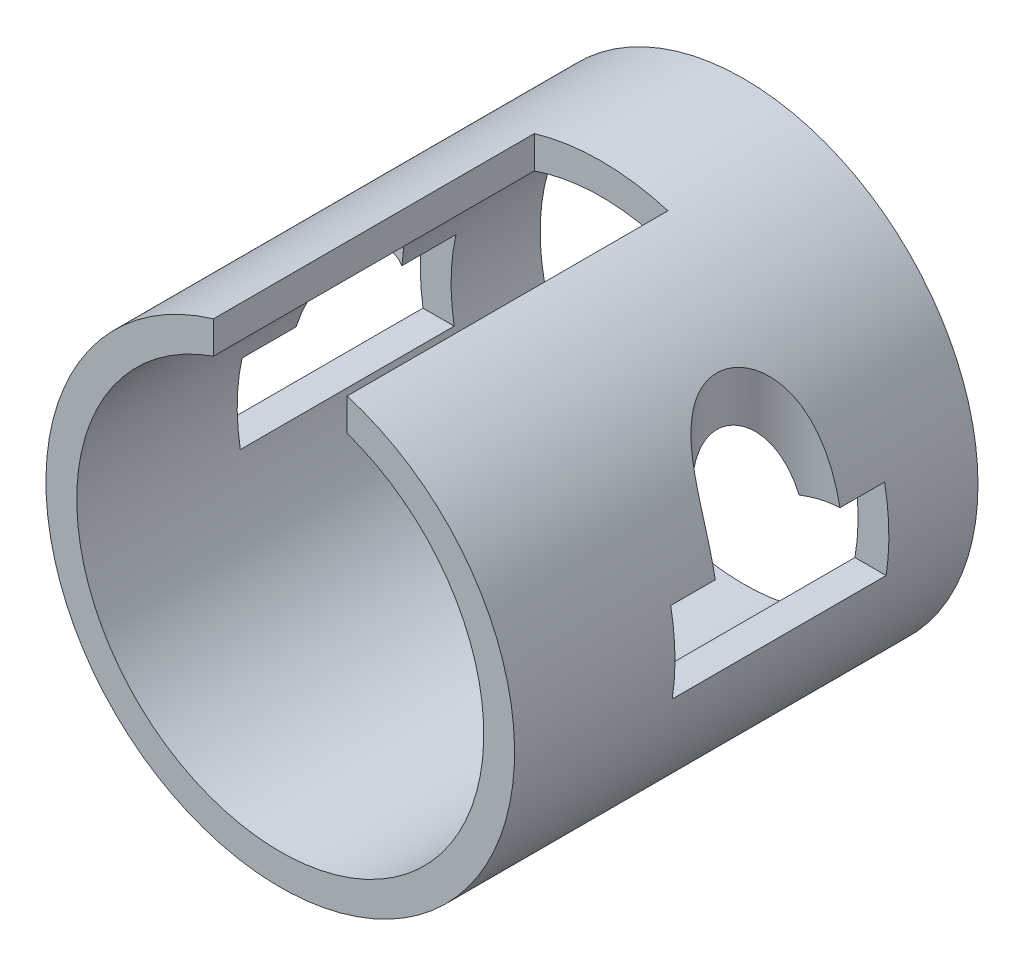
SolidWorks part; units mm, degrees
material "PVC Rigid"
ref_plane "Front Plane" through (0, 0, 0) normal (0, 0, 1) x (1, 0, 0)
ref_plane "Top Plane" through (0, 0, 0) normal (0, 1, 0) x (1, 0, 0)
ref_plane "Right Plane" through (0, 0, 0) normal (1, 0, 0) x (0, 0, -1)
sketch "Sketch1" plane through (0, 0, 0) normal (0, 0, 1) x (1, 0, 0)
  circle A0 centre (0, 0) radius 83.4771
  circle A2 centre (0, 0) radius 72.5043
  point P3 (0, 0)
  point P10 (0, 0)
  dimension "D1" = 10.9728
  dimension "D2" = 145.0086
extrude "Boss-Extrude1" add sketch "Sketch1" along normal mid plane 165.1
sketch "Sketch2" plane through (0, 0, 0) normal (0, 1, 0) x (1, 0, 0)
  line L0 (-23.8125, 31.75) -> (0, 0) construction
  line L1 (-23.8125, 31.75) -> (23.8125, 31.75)
  line L2 (-23.8125, 31.75) -> (-23.8125, -82.55)
  line L3 (-23.8125, -82.55) -> (23.8125, -82.55)
  line L4 (23.8125, 31.75) -> (23.8125, -82.55)
  line L5 (-23.8125, 31.75) -> (23.8125, -82.55) construction
  line L6 (-23.8125, -82.55) -> (23.8125, 31.75) construction
  line L7 (0, 0) -> (23.8125, 31.75) construction
  line L8 (-83.4771, -82.55) -> (83.4771, -82.55) construction
  point P0 (0, -25.4)
  dimension "D1" = 47.625
  dimension "D2" = 0
  dimension "D3" = 114.3
extrude "Cut-Extrude1" cut sketch "Sketch2" along normal through all
sketch "Sketch3" plane through (0, 0, 0) normal (1, 0, 0) x (0, 0, -1)
  line L0 (-82.55, 80.0087) -> (-82.55, -83.4771) construction
  line L1 (50.8, 12.7) -> (-25.4, 12.7) construction
  line L2 (50.8, 12.7) -> (50.8, -12.7)
  line L3 (50.8, -12.7) -> (-25.4, -12.7)
  line L4 (-25.4, 12.7) -> (-25.4, -12.7)
  line L5 (50.8, 12.7) -> (-25.4, -12.7) construction
  line L6 (50.8, -12.7) -> (-25.4, 12.7) construction
  line L7 (-25.4, 12.7) -> (0, 0) construction
  line L8 (0, 0) -> (-25.4, -12.7) construction
  line L9 (50.8, 12.7) -> (-25.4, 12.7)
  point P0 (12.7, 0)
  dimension "D1" = 57.15
  dimension "D2" = 76.2
  dimension "D3" = 25.4
extrude "Cut-Extrude2" cut sketch "Sketch3" against normal through all both and the other way through all
sketch "Sketch4" plane through (0, -12.7, 0) normal (0, 1, 0) x (1, 0, 0)
  line L0 (-71.3834, 12.7) -> (-82.5054, 12.7) construction
  line L1 (-71.3834, -25.4) -> (-71.3834, 50.8) construction
  line L2 (71.3834, 12.7) -> (82.5054, 12.7) construction
  line L3 (71.3834, 50.8) -> (71.3834, -25.4) construction
  line L4 (-82.5054, -25.4) -> (-82.5054, 50.8) construction
  circle A0 centre (-82.5054, 12.7) radius 22.225
  circle A1 centre (82.5054, 12.7) radius 22.225
  dimension "D2" = 44.45
extrude "Cut-Extrude3" cut sketch "Sketch4" along normal through all
sketch "Sketch6" plane through (0, 0, 0) normal (1, 0, 0) x (0, 0, -1)
  line L0 (50.8, 12.7) -> (50.8, -12.7) construction
  line L1 (-25.4, 12.7) -> (50.8, 12.7)
  line L2 (-25.4, 12.7) -> (-25.4, 15.875)
  line L3 (-25.4, 15.875) -> (50.8, 15.875)
  line L4 (50.8, 12.7) -> (50.8, 15.875)
  line L5 (-25.4, -12.7) -> (-25.4, 12.7) construction
  line L9 (-25.4, 12.7) -> (-6.5419, 12.7) construction
  dimension "D1" = 3.175
extrude "Cut-Extrude4" cut sketch "Sketch6" against normal through all both and the other way through all
ref_point "Point1"
